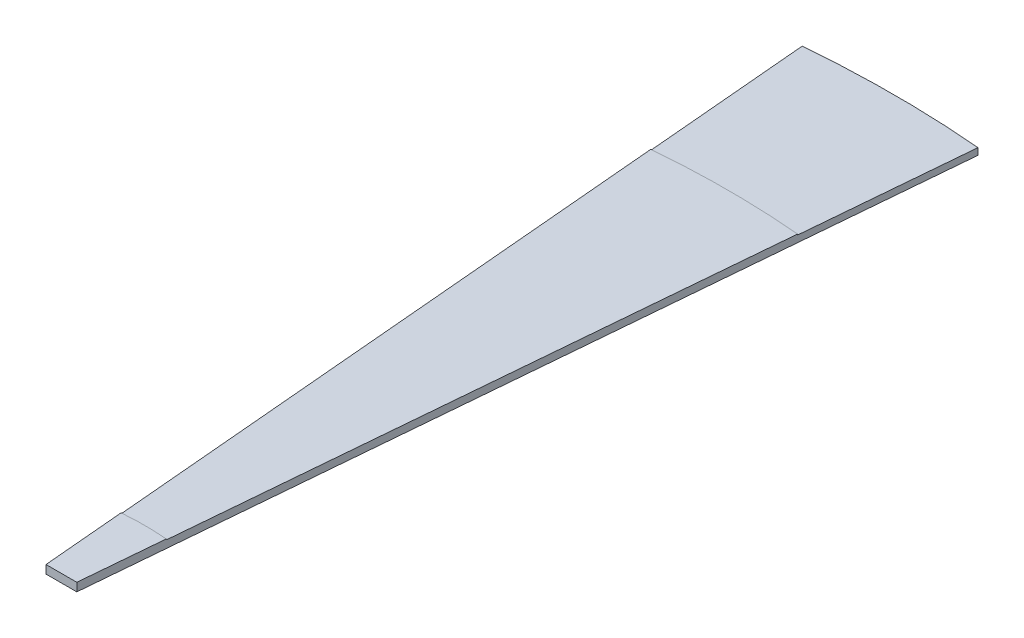
SolidWorks part; units mm, degrees
ref_plane "Plan de face" through (0, 0, 0) normal (0, 0, 1) x (1, 0, 0)
ref_plane "Plan de dessus" through (0, 0, 0) normal (0, 1, 0) x (1, 0, 0)
ref_plane "Plan de droite" through (0, 0, 0) normal (1, 0, 0) x (0, 0, -1)
sketch "Esquisse1" plane through (0, 0, 0) normal (0, 1, 0) x (1, 0, 0)
  line L0 (0, 0) -> (0, 100) construction
  line L1 (18.5, 0) -> (-18.5, 0)
  line L2 (-18.5, 0) -> (-27.1452, 98.8148)
  line L3 (-18.5, 0) -> (0, -211.456) construction
  line L4 (18.5, 0) -> (27.1452, 98.8148)
  line L5 (18.5, 0) -> (0, -211.456) construction
  arc A0 (-27.1452, 98.8148) -> (27.1452, 98.8148) centre (0, -211.456) cw
  point P9 (0, 100)
  dimension "D1" = 18.5
  dimension "D2" = 10
  dimension "D3" = 100
extrude "Extrusion1" add sketch "Esquisse1" along normal blind 10
sketch "Esquisse2" plane through (0, 0, 0) normal (0, -1, 0) x (1, 0, 0)
  line L0 (-27.1452, -98.8148) -> (-88.1542, -796.1511)
  line L1 (0, 0) -> (0, -800) construction
  line L2 (27.1452, -98.8148) -> (88.1542, -796.1511)
  line L3 (18.5, 0) -> (27.1452, -98.8148) construction
  line L4 (-27.1452, -98.8148) -> (-18.5, 0) construction
  line L5 (0, 211.456) -> (0, 231.0628) construction
  line L6 (-27.1452, -98.8148) -> (0, 211.456) construction
  line L7 (0, 211.456) -> (27.1452, -98.8148) construction
  arc A0 (-27.1452, -98.8148) -> (27.1452, -98.8148) centre (0, 211.456) ccw
  arc A1 (-88.1542, -796.1511) -> (88.1542, -796.1511) centre (0, 211.456) ccw
  dimension "D1" = 800
extrude "Extrusion2" add sketch "Esquisse2" against normal blind 9
sketch "Esquisse5" plane through (0, 0, 0) normal (0, -1, 0) x (1, 0, 0)
  line L0 (-88.1542, -796.1511) -> (-105.5853, -995.39)
  line L1 (88.1542, -796.1511) -> (105.5853, -995.39)
  line L2 (18.5, 0) -> (88.1542, -796.1511) construction
  line L3 (-88.1542, -796.1511) -> (-18.5, 0) construction
  arc A0 (-88.1542, -796.1511) -> (88.1542, -796.1511) centre (0, 211.456) ccw
  arc A1 (-88.1542, -796.1511) -> (88.1542, -796.1511) centre (0, 211.456) ccw construction
  arc A2 (-105.5853, -995.39) -> (105.5853, -995.39) centre (0, 211.456) ccw
  point P15 (0, -1000)
  dimension "D1" = 1000
extrude "Extrusion3" add sketch "Esquisse5" against normal blind 8
